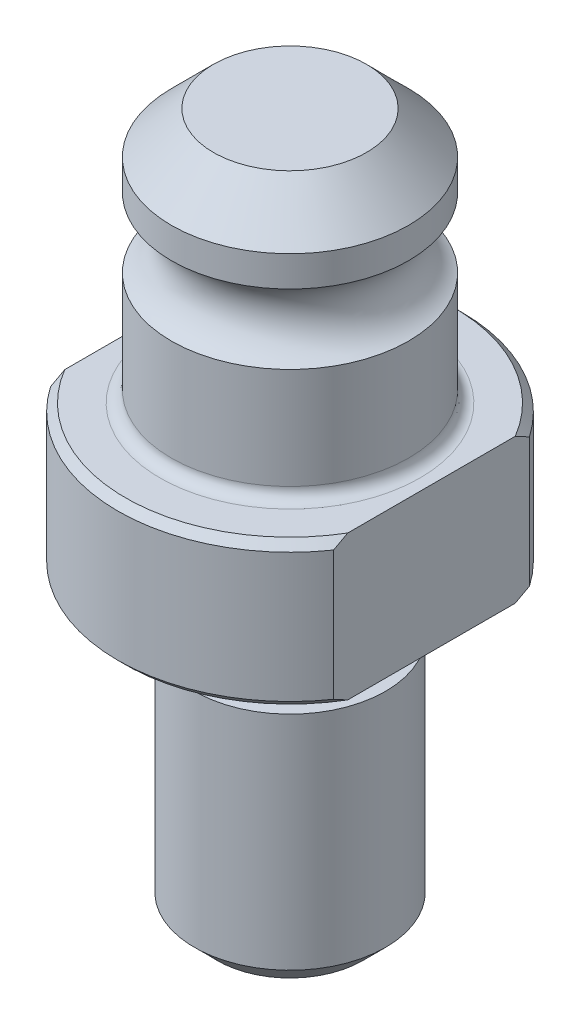
SolidWorks part; units mm, degrees
ref_plane "Front Plane" through (0, 0, 0) normal (0, 0, 1) x (1, 0, 0)
ref_plane "Top Plane" through (0, 0, 0) normal (0, 1, 0) x (1, 0, 0)
ref_plane "Right Plane" through (0, 0, 0) normal (1, 0, 0) x (0, 0, -1)
sketch "Sketch1" plane through (0, 0, 0) normal (0, 0, 1) x (1, 0, 0)
  line L0 (0, 26.543) -> (0, -20.066)
  line L1 (0, -20.066) -> (-6.35, -20.066)
  line L2 (-6.35, -20.066) -> (-6.35, -3.81)
  line L3 (-6.35, -3.81) -> (-5.1943, -3.81)
  line L4 (-5.1943, -3.81) -> (-5.1943, -1.27)
  line L5 (-6.4643, 0) -> (-11.43, 0)
  line L6 (-11.43, 0) -> (-11.43, 9.6012)
  line L7 (-11.43, 9.6012) -> (-7.874, 9.6012)
  line L8 (-7.874, 9.6012) -> (-7.874, 17.0942)
  line L9 (-7.874, 23.749) -> (-5.08, 26.543)
  line L10 (-5.08, 26.543) -> (0, 26.543)
  line L11 (0, -20.066) -> (0, -73.6863) construction
  line L12 (-7.874, 21.717) -> (-7.874, 23.749)
  arc A0 (-7.874, 17.0942) -> (-7.874, 21.717) centre (-8.8648, 19.4056) ccw
  arc A1 (-6.4643, 0) -> (-5.1943, -1.27) centre (-6.4643, -1.27) cw
  dimension "D13" = 12.7
  dimension "D14" = 1.27
  dimension "D1" = 12.7
  dimension "D2" = 10.3886
  dimension "D3" = 22.86
  dimension "D4" = 15.748
  dimension "D5" = 20.066
  dimension "D6" = 9.6012
  dimension "D7" = 3.81
  dimension "D8" = 45
  dimension "D9" = 10.16
  dimension "D10" = 26.543
  dimension "D11" = 7.493
  dimension "D12" = 4.6228
revolve "Revolve1" add sketch "Sketch1" angle 360 about L11
chamfer "Chamfer1" distance 0.508 angle 45 2 edges at (-11.43, 0, 0) (-11.43, 9.6012, 0)
chamfer "Chamfer2" distance 1.524 angle 45 1 edges at (-6.35, -20.066, 0)
sketch "Sketch2" plane through (0, 9.6012, 0) normal (0, 1, 0) x (1, 0, 0)
  line L0 (-9.398, 6.5056) -> (-9.398, -6.5056)
  line L1 (9.398, 6.5056) -> (9.398, -6.5056)
  circle A0 centre (0, 0) radius 11.43 construction
  arc A1 (9.398, -6.5056) -> (9.398, 6.5056) centre (0, 0) ccw
  arc A2 (-9.398, 6.5056) -> (-9.398, -6.5056) centre (0, 0) ccw
  dimension "D1" = 9.398
  dimension "D2" = 9.398
extrude "Cut-Extrude1" cut sketch "Sketch2" against normal through all
fillet "Fillet1" radius 0.762 1 edges at (-7.874, 9.6012, 0)
